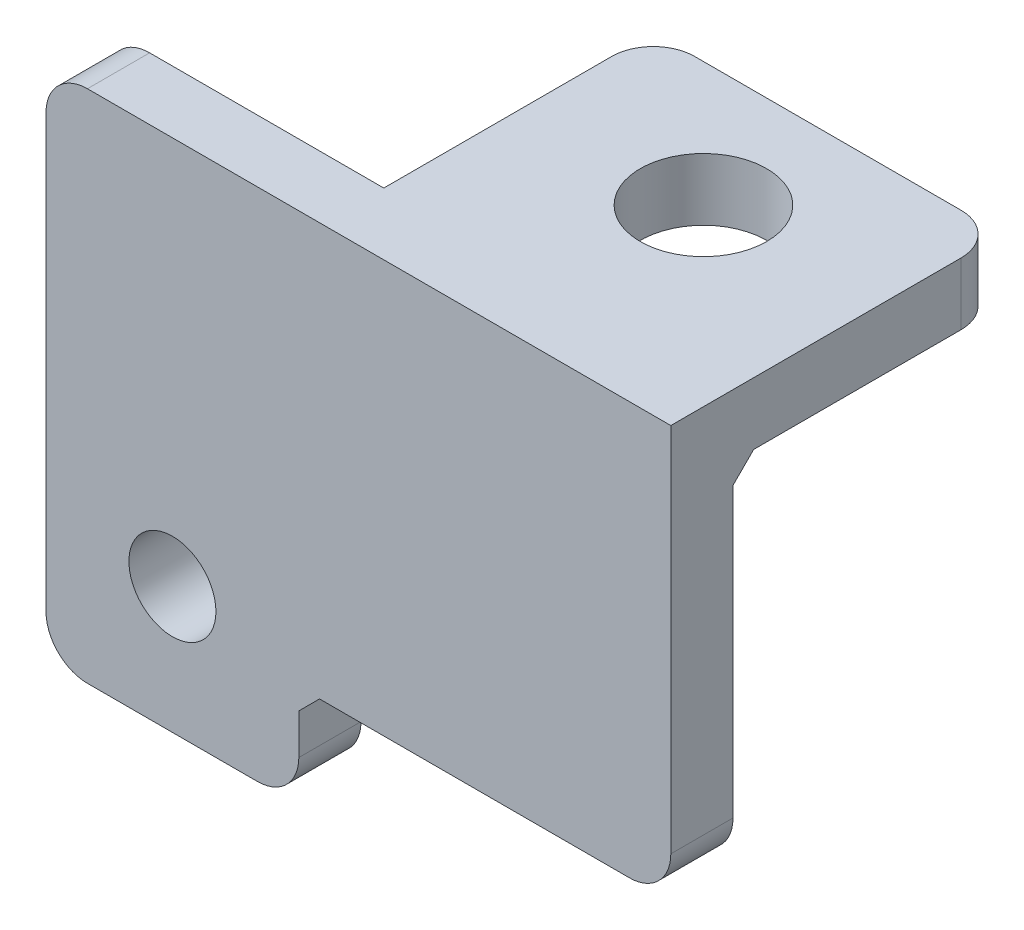
SolidWorks part; units mm, degrees
ref_plane "Front Plane" through (0, 0, 0) normal (0, 0, 1) x (1, 0, 0)
ref_plane "Top Plane" through (0, 0, 0) normal (0, 1, 0) x (1, 0, 0)
ref_plane "Right Plane" through (0, 0, 0) normal (1, 0, 0) x (0, 0, -1)
sketch "Sketch1" plane through (0, 0, 0) normal (0, 0, 1) x (1, 0, 0)
  line L4 (28.7, 57.75) -> (12.7, 57.75) construction
  line L5 (-5.2, 77.75) -> (7, 77.75)
  line L6 (-5.2, 77.75) -> (-5.2, 52.9)
  line L7 (-5.2, 52.9) -> (7, 52.9)
  line L8 (7, 57.85) -> (7, 52.9)
  line L9 (7, 57.85) -> (24.95, 57.85)
  line L10 (24.95, 57.85) -> (24.95, 77.75)
  line L11 (24.95, 77.75) -> (7, 77.75)
  line L13 (29.95, 150.95) -> (29.95, -3.05) construction
  circle A0 centre (0.9, 59) radius 2.1 construction
  circle A1 centre (0.9, 59) radius 2.1
  point P11 (18.8304, 72.75)
  point P14 (0, 0)
  point P15 (0, 0)
  dimension "D3" = 4
  dimension "D1" = 4
  dimension "D2" = 4
  dimension "D4" = 20
  dimension "D5" = 0.1
  dimension "D6" = 5
extrude "Boss-Extrude1" add sketch "Sketch1" along normal blind 3
sketch "Sketch2" plane through (-52.8, 77.75, 0) normal (0, -1, 0) x (0, 0, -1)
  line L1 (-3, 77.75) -> (13, 77.75)
  line L2 (-3, 77.75) -> (-3, 60.9)
  line L3 (-3, 60.9) -> (13, 60.9)
  line L4 (13, 77.75) -> (13, 60.9)
  line L7 (13, 60.8) -> (-40.4, 60.8) construction
  line L8 (16, 63.7) -> (16, 83.7) construction
  point P4 (-2, 72.75)
  point P5 (11.7749, 61.4793)
  point P7 (11.4538, 72.75)
  point P8 (12.1272, 81.6)
  point P9 (0, 0)
  dimension "D1" = 0.1
  dimension "D2" = 3
extrude "Boss-Extrude2" add sketch "Sketch2" along normal blind 3
sketch "Sketch4" plane through (0, 0, 0) normal (0, 0, -1) x (-1, 0, 0)
  line L0 (-7, 57.85) -> (-24.95, 57.85) construction
  line L1 (-21.95, 57.85) -> (-16.4, 57.85)
  line L2 (-21.95, 57.85) -> (-21.95, 58.85)
  line L3 (-21.95, 58.85) -> (-16.4, 58.85)
  line L4 (-16.4, 57.85) -> (-16.4, 58.85)
  line L5 (-24.95, 57.85) -> (-24.95, 74.75) construction
  point P4 (-21.6169, 57.85)
  point P5 (0, 0)
  dimension "D1" = 5.55
  dimension "D2" = 1
  dimension "D3" = 3
extrude "Boss-Extrude3" add sketch "Sketch4" along normal blind 3
chamfer "Chamfer1" distance 1 angle 45 3 edges at (7, 57.85, 1.5) (16.525, 74.75, 0) (19.175, 58.85, 0)
sketch "Sketch3" plane through (0, 74.75, 0) normal (0, -1, 0) x (0, 0, -1)
  line L0 (13, 24.95) -> (13, 8.1) construction
  line L1 (1, 24.95) -> (13, 24.95) construction
  circle A0 centre (7, 16.525) radius 3.05
  point P4 (0, 0)
  point P5 (13, 16.525)
  point P8 (7, 24.95)
  dimension "D1" = 6.1
extrude "Cut-Extrude1" cut sketch "Sketch3" against normal through all
fillet "Fillet1" radius 2 6 edges at (8.1, 76.25, -13) (24.95, 76.25, -13) (-5.2, 77.75, 1.5) (-5.2, 52.9, 1.5) (7, 52.9, 1.5) (24.95, 57.85, 1.5)
